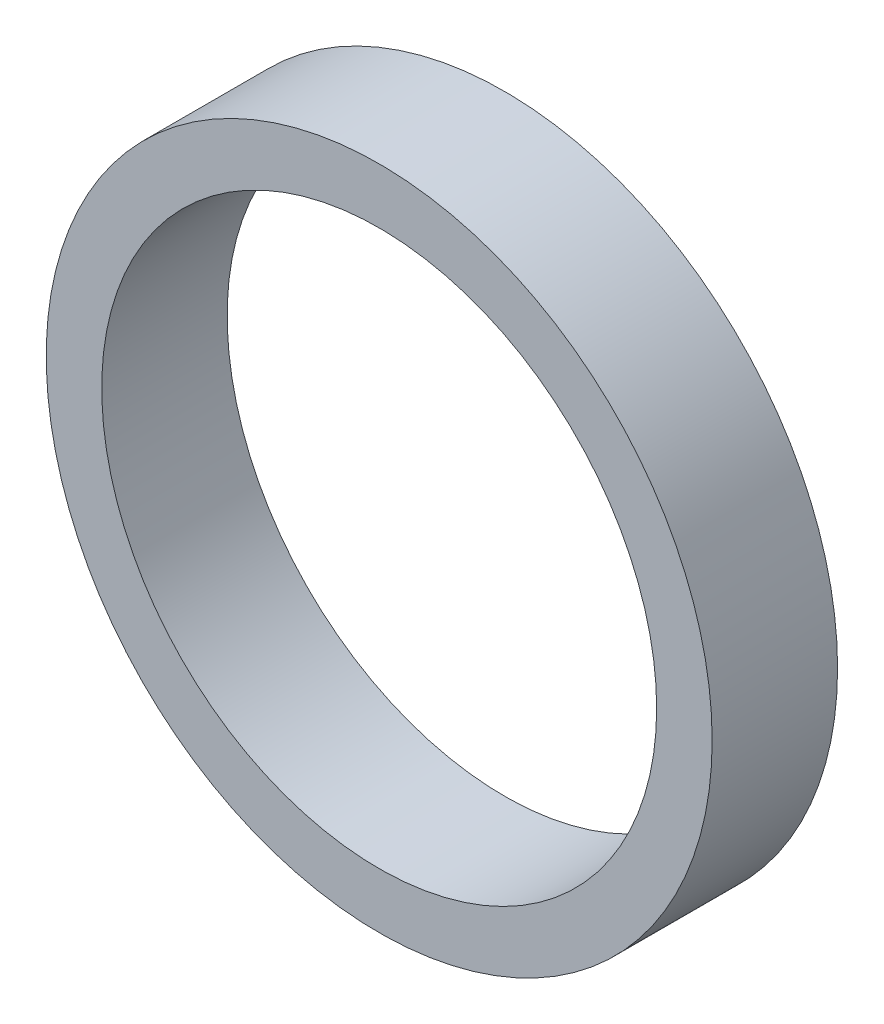
SolidWorks part; units mm, degrees
material "6063-T6"
ref_plane "Płaszczyzna XY" through (0, 0, 0) normal (0, 0, 1) x (1, 0, 0)
ref_plane "Płaszczyzna XZ" through (0, 0, 0) normal (0, 1, 0) x (1, 0, 0)
ref_plane "Płaszczyzna YZ" through (0, 0, 0) normal (1, 0, 0) x (0, 0, -1)
sketch "Szkic1" plane through (0, 0, 0) normal (0, 0, 1) x (1, 0, 0)
  circle A2 centre (0, 0) radius 15
  circle A3 centre (0, 0) radius 12.5
  dimension "D1" = 30
  dimension "D2" = 25
extrude "Dodanie-wyciągnięcie1" add sketch "Szkic1" along normal blind 5.65
